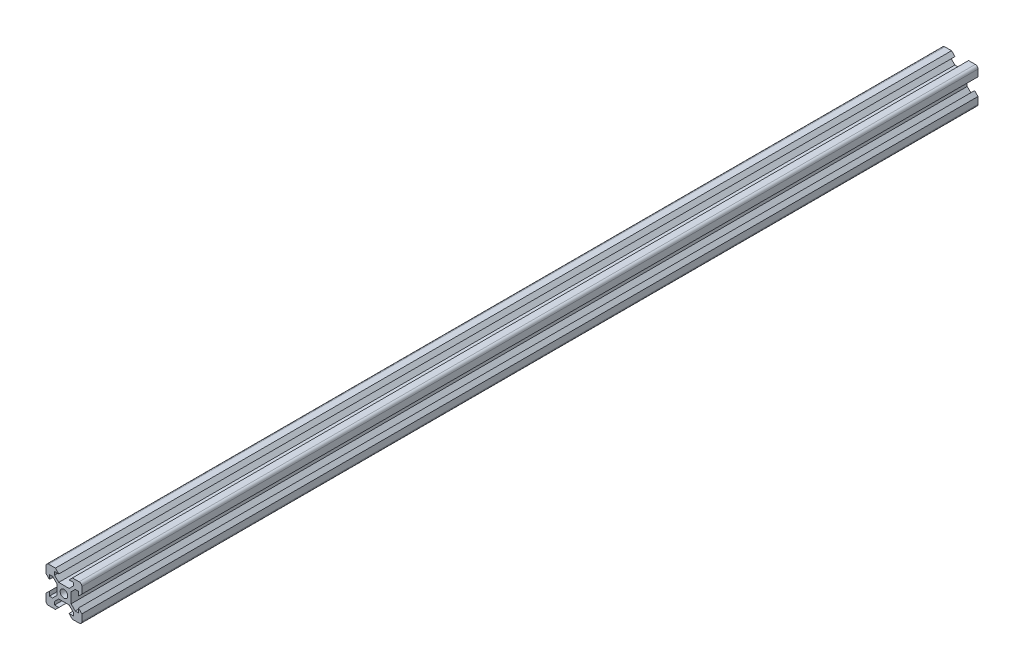
SolidWorks part; units mm, degrees
material "6061 Alloy"
ref_plane "Front Plane" through (0, 0, 0) normal (0, 0, 1) x (1, 0, 0)
ref_plane "Top Plane" through (0, 0, 0) normal (0, 1, 0) x (1, 0, 0)
ref_plane "Right Plane" through (0, 0, 0) normal (1, 0, 0) x (0, 0, -1)
sketch "Sketch1" plane through (0, 0, 0) normal (0, 0, 1) x (1, 0, 0)
  line L0 (15.6876, 55.3211) -> (115.0437, 55.3211) construction
  line L1 (8.1, 5.225) -> (8.1, 2.85)
  line L2 (-8.5, 10) -> (-4.75, 10)
  line L3 (-10, 8.5) -> (-10, 4.75)
  line L4 (-8.5, -10) -> (-4.75, -10)
  line L5 (10, 8.5) -> (10, 4.75)
  line L6 (6.325, 5.225) -> (4, 2.9)
  line L7 (-8.1, -2.85) -> (-8.1, -5.225)
  line L8 (-2.9, 4) -> (2.9, 4)
  line L9 (-4, 2.9) -> (-4, -2.9)
  line L10 (-2.9, -4) -> (2.9, -4)
  line L11 (4, 2.9) -> (4, -2.9)
  line L12 (2.85, -8.1) -> (5.225, -8.1)
  line L13 (-5.225, -8.1) -> (-2.85, -8.1)
  line L14 (5.225, 6.325) -> (2.9, 4)
  line L17 (-10, 4.75) -> (-8.1, 2.85)
  line L20 (4.75, -10) -> (8.5, -10)
  line L22 (-10, -4.75) -> (-10, -8.5)
  line L23 (10, -4.75) -> (10, -8.5)
  line L24 (-10, -4.75) -> (-8.1, -2.85)
  line L25 (-4.75, -10) -> (-2.85, -8.1)
  line L26 (4.75, -10) -> (2.85, -8.1)
  line L27 (10, -4.75) -> (8.1, -2.85)
  line L28 (10, 4.75) -> (8.1, 2.85)
  line L29 (-4.75, 10) -> (-2.85, 8.1)
  line L30 (4.75, 10) -> (2.85, 8.1)
  line L31 (8.1, -2.85) -> (8.1, -5.225)
  line L32 (6.325, -5.225) -> (8.1, -5.225)
  line L33 (5.225, -6.325) -> (5.225, -8.1)
  line L34 (4.75, 10) -> (8.5, 10)
  line L35 (2.85, 8.1) -> (5.225, 8.1)
  line L36 (10, -10) -> (10.975, -10.975) construction
  line L37 (-5.225, 8.1) -> (-2.85, 8.1)
  line L38 (-8.1, -5.225) -> (-6.325, -5.225)
  line L39 (-5.225, 6.325) -> (-2.9, 4)
  line L40 (-8.1, 5.225) -> (-8.1, 2.85)
  line L41 (-5.225, -6.325) -> (-5.225, -8.1)
  line L42 (-6.325, 5.225) -> (-4, 2.9)
  line L46 (-8.1, 5.225) -> (-6.325, 5.225)
  line L47 (-5.225, 8.1) -> (-5.225, 6.325)
  line L52 (8.1, 5.225) -> (6.325, 5.225)
  line L53 (5.225, 8.1) -> (5.225, 6.325)
  line L63 (4, -2.9) -> (6.325, -5.225)
  line L66 (2.9, -4) -> (5.225, -6.325)
  line L67 (-2.9, -4) -> (-5.225, -6.325)
  line L70 (-4, -2.9) -> (-6.325, -5.225)
  arc A0 (-8.5, -10) -> (-10, -8.5) centre (-8.5, -8.5) cw
  arc A1 (8.5, -10) -> (10, -8.5) centre (8.5, -8.5) ccw
  arc A2 (10, 8.5) -> (8.5, 10) centre (8.5, 8.5) ccw
  arc A3 (-8.5, 10) -> (-10, 8.5) centre (-8.5, 8.5) ccw
  circle A4 centre (0, 0) radius 2.125
  point P2 (0, 0)
  point P8 (0, 0)
  point P14 (-10, -10)
  point P20 (0, 0)
  point P49 (10, 10)
  point P52 (-10, 10)
  dimension "D3" = 1.5
  dimension "D4" = 4.25
  dimension "D1" = 20
  dimension "D2" = 20
  dimension "D13" = 5.25
  dimension "D14" = 5.25
  dimension "D15" = 90
  dimension "D16" = 5.25
  dimension "D17" = 5.25
  dimension "D18" = 5.25
  dimension "D19" = 5.25
  dimension "D20" = 5.25
  dimension "D21" = 5.25
  dimension "D22" = 90
  dimension "D23" = 90
  dimension "D24" = 90
  dimension "D25" = 2.85
  dimension "D26" = 2.85
  dimension "D27" = 2.85
  dimension "D28" = 2.85
extrude "Boss-Extrude1" add sketch "Sketch1" along normal blind 500
